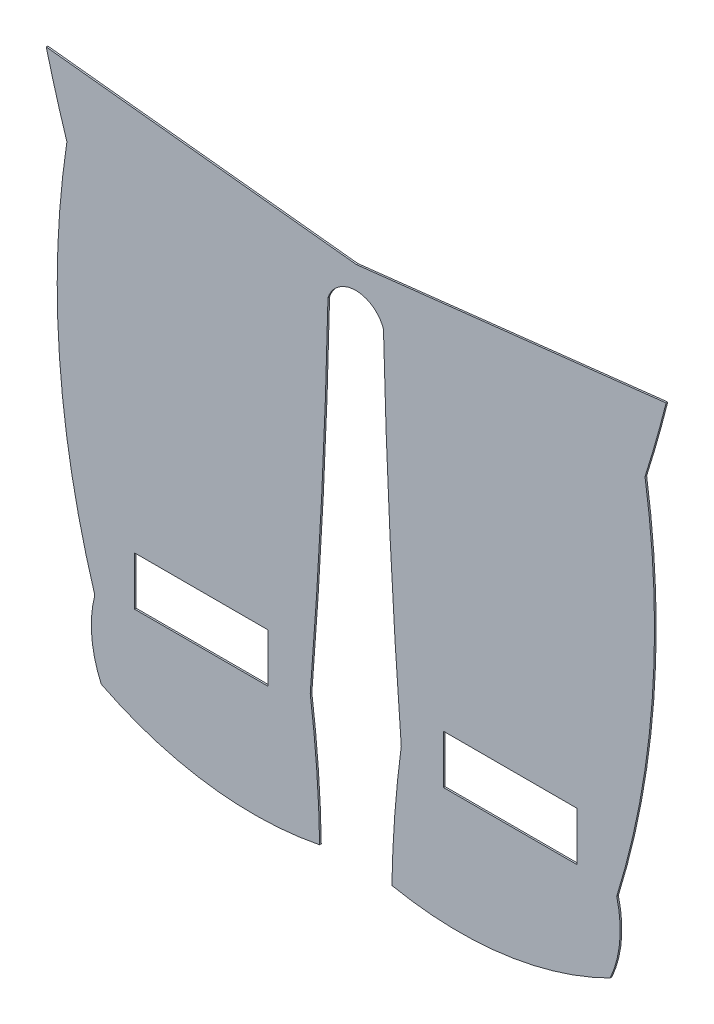
SolidWorks part; units mm, degrees
ref_plane "Alzado" through (0, 0, 0) normal (0, 0, 1) x (1, 0, 0)
ref_plane "Planta" through (0, 0, 0) normal (0, 1, 0) x (1, 0, 0)
ref_plane "Vista lateral" through (0, 0, 0) normal (1, 0, 0) x (0, 0, -1)
sketch "Model" plane through (0, 0, 0) normal (0, 0, 1) x (1, 0, 0)
  line L0 (38.1333, 3.0188) -> (57.1799, 5.1732)
  line L1 (19.0575, 5.0724) -> (38.1333, 3.0188)
  line L2 (32.69, -22.1573) -> (24.49, -22.1573)
  line L3 (32.69, -19.1573) -> (32.69, -22.1573)
  line L4 (24.49, -19.1573) -> (32.69, -19.1573)
  line L5 (24.49, -22.1573) -> (24.49, -19.1573)
  line L6 (51.69, -22.1573) -> (43.49, -22.1573)
  line L7 (51.69, -19.1573) -> (51.69, -22.1573)
  line L8 (43.49, -19.1573) -> (51.69, -19.1573)
  line L9 (43.49, -22.1573) -> (43.49, -19.1573)
  arc A0 (40.3143, -28.9598) -> (53.7414, -27.1744) centre (44.4432, -8.6299) ccw
  arc A1 (22.4432, -27.1765) -> (35.8714, -29.0171) centre (31.8199, -8.6716) ccw
  arc A2 (35.8714, -29.0171) -> (35.2923, -21.2573) centre (-31.3276, -30.1309) ccw
  arc A3 (35.2923, -21.2573) -> (36.3832, 0.3783) centre (-340.4557, 8.5331) ccw
  arc A4 (39.7967, 0.4134) -> (36.3832, 0.3783) centre (38.0958, -0.1792) ccw
  arc A5 (39.7967, 0.4134) -> (40.8915, -21.2567) centre (446.1092, 10.078) ccw
  arc A6 (40.8915, -21.2567) -> (40.3143, -28.9598) centre (107.513, -30.1219) ccw
  arc A7 (53.7414, -27.1744) -> (54.1416, -22.6252) centre (47.4422, -24.3281) ccw
  arc A8 (54.1416, -22.6252) -> (55.882, 0.5985) centre (4.163, -7.2026) ccw
  arc A9 (55.882, 0.5985) -> (57.1799, 5.1732) centre (-22.2255, 25.2303) ccw
  arc A10 (19.0575, 5.0724) -> (20.3281, 0.6583) centre (89.8499, 23.0607) ccw
  arc A11 (20.3281, 0.6583) -> (22.0424, -22.6275) centre (72.1701, -7.2311) ccw
  arc A12 (22.0424, -22.6275) -> (22.4432, -27.1765) centre (28.7419, -24.3295) ccw
extrude "Saliente-Extruir1" add sketch "Model" along normal blind 0.1
